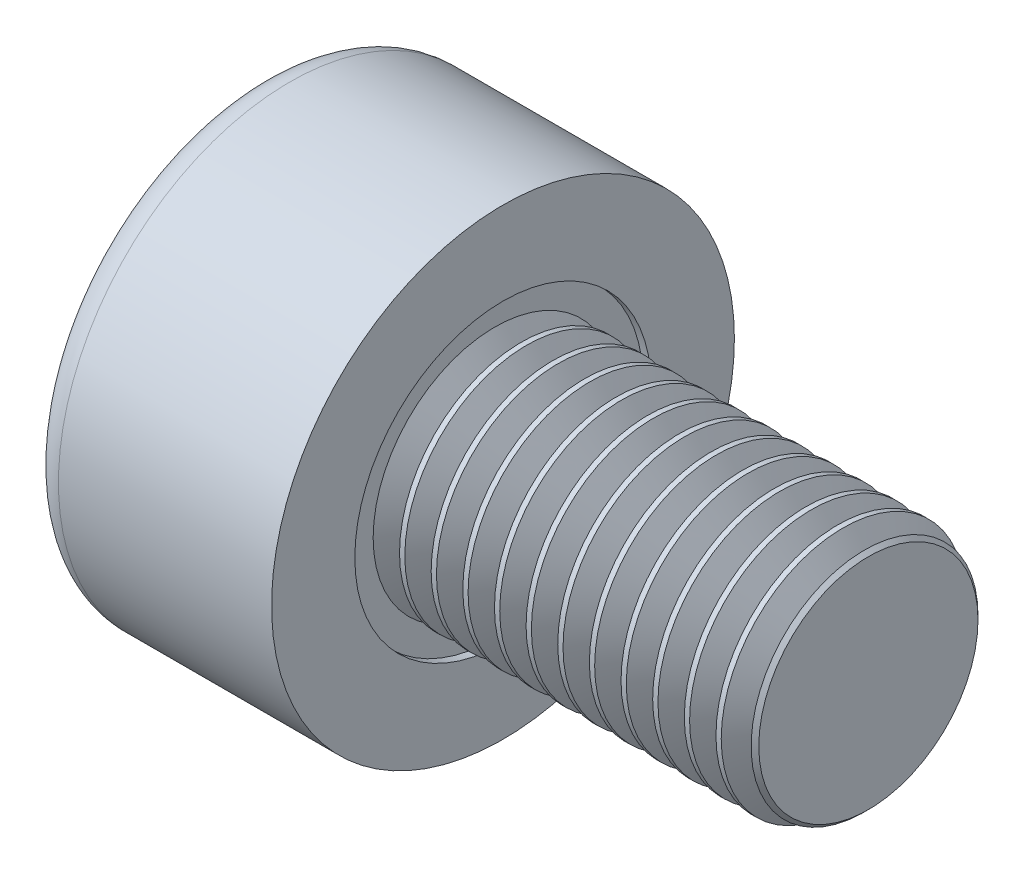
SolidWorks part; units mm, degrees
ref_plane "Front" through (0, 0, 0) normal (0, 0, 1) x (1, 0, 0)
ref_plane "Top" through (0, 0, 0) normal (0, 1, 0) x (1, 0, 0)
ref_plane "Right" through (0, 0, 0) normal (1, 0, 0) x (0, 0, -1)
sketch "Sketch1" plane through (0, 0, 0) normal (1, 0, 0) x (0, 0, -1)
  circle A0 centre (0, 0) radius 1.9
  dimension "dk" = 3.8
extrude "BaseHead" add sketch "Sketch1" along normal blind 2
sketch "Sketch2" plane through (2, 0, 0) normal (1, 0, 0) x (0, 0, -1)
  circle A0 centre (0, 0) radius 1
  dimension "d" = 2
extrude "BaseBody" add sketch "Sketch2" along normal blind 3
cosmetic thread "ThreadCosmetic1" [suppressed] parameters "b"=3, "D2"=1.567
sketch "Sketch3" plane through (0, 0, 0) normal (1, 0, 0) x (0, 0, -1)
  line L1 (0.866, 0) -> (0.433, 0.75)
  line L2 (0.433, 0.75) -> (-0.433, 0.75)
  line L3 (-0.433, 0.75) -> (-0.866, 0)
  line L4 (-0.866, 0) -> (-0.433, -0.75)
  line L5 (-0.433, -0.75) -> (0.433, -0.75)
  line L6 (0.433, -0.75) -> (0.866, 0)
  circle A0 centre (0, 0) radius 0.75 construction
  dimension "s" = 1.5
  dimension "e" = 1.7321
extrude "HexagonSocket" cut sketch "Sketch3" along normal blind 1
sketch "Sketch4" plane through (-4.1961, 0.75, 0) normal (0, 0, 1) x (-1, 0, 0)
  line L0 (-5.1961, 1.5) -> (-5.6292, 0.75)
  line L2 (-5.6292, 0.75) -> (-5.1961, 0.75)
  line L3 (-5.1961, 0.75) -> (-5.1961, 1.5)
  line L4 (-5.0351, 0.75) -> (0.839, 0.75) construction
  line L5 (-9.1961, 0.75) -> (-6.1961, 0.75) construction
  line L6 (-6.1961, 0.75) -> (-4.1961, 0.75) construction
  dimension "m" = 60
revolve "Cut-Revolve1" cut sketch "Sketch4" angle 360 about L4
fillet "HeadFillet" [suppressed] radius 0.1
fillet "TopFillet" radius 0.25 1 edges at (0, 0, -1.9)
chamfer "Chamfer1" distance 0.1 angle 45 1 edges at (5, 0, -1)
sketch "Sketch5" plane through (0, 0, 0) normal (0, 0, 1) x (1, 0, 0)
  line L0 (4.9, 0.8125) -> (5.0083, 1)
  line L1 (5.0083, 1) -> (5.0083, 1.2165)
  line L2 (5.0083, 1.2165) -> (4.7918, 1.2165)
  line L3 (4.7918, 1.2165) -> (4.7918, 1)
  line L4 (4.7918, 1) -> (4.9, 0.8125)
  line L5 (0, 0) -> (7.8886, 0) construction
  line L6 (4.9, -1) -> (4.9, 1) construction
  dimension "D1" = 2
  dimension "D2" = 0.2165
revolve "Cut-Revolve10" cut sketch "Sketch5" angle 360 about L5
pattern_linear "LPattern10" count 12 spacing 0.2598 along (-1, 0, 0) of "Cut-Revolve10"
equation "\"r1@TopFillet\" = \"d@Sketch2\" / 8"
equation "\"D1@Chamfer1\" = \"r@HeadFillet\""
equation "\"D1@Sketch5\" = \"d@Sketch2\""
equation "\"D2@Sketch5\" =  ( \"d@Sketch2\" - \"D2@ThreadCosmetic1\" )  / 2"
equation "\"D3@LPattern10\" = \"D2@Sketch5\" * 1.2"
equation "\"D1@LPattern10\" = \"b@ThreadCosmetic1\" / \"D3@LPattern10\""
